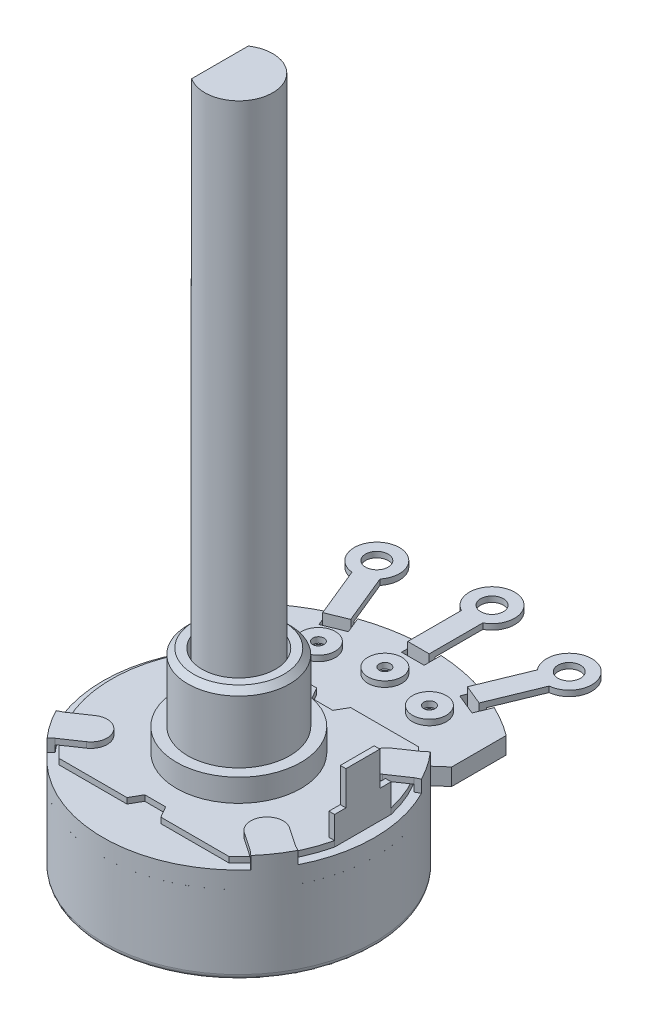
SolidWorks part; units mm, degrees
ref_plane "Front Plane" through (0, 0, 0) normal (0, 0, 1) x (1, 0, 0)
ref_plane "Top Plane" through (0, 0, 0) normal (0, 1, 0) x (1, 0, 0)
ref_plane "Right Plane" through (0, 0, 0) normal (1, 0, 0) x (0, 0, -1)
sketch "Sketch1" plane through (0, 0, 0) normal (0, 1, 0) x (1, 0, 0)
  circle A0 centre (0, 0) radius 12
  dimension "D1" = 24
extrude "Boss-Extrude1" add sketch "Sketch1" along normal blind 7
sketch "Sketch2" plane through (0, 7, 0) normal (0, 1, 0) x (1, 0, 0)
  circle A0 centre (0, 0) radius 11.5
  circle A1 centre (0, 0) radius 12 construction
  dimension "D1" = 0.5
extrude "Cut-Extrude1" cut sketch "Sketch2" against normal blind 6.5
sketch "Sketch3" plane through (0, 7, 0) normal (0, 1, 0) x (1, 0, 0)
  line L0 (0, 0) -> (-13.6067, 12) construction
  line L1 (-13.6067, 12) -> (13.6067, 12) construction
  line L2 (13.6067, 12) -> (0, 0) construction
  line L3 (0, 0) -> (0, 11.5) construction
  line L4 (-9, 7.9373) -> (9, 7.9373) construction
  line L5 (-9, 7.9373) -> (0, 0)
  line L6 (0, 0) -> (9, 7.9373)
  circle A0 centre (0, 0) radius 11.5 construction
  circle A1 centre (0, 0) radius 12 construction
  arc A3 (9, 7.9373) -> (-9, 7.9373) centre (0, 0) ccw
  dimension "D1" = 18
extrude "Cut-Extrude2" cut sketch "Sketch3" against normal blind 2
ref_plane "Plane1" through (0, 7.001, 0) normal (0, 1, 0) x (1, 0, 0)
sketch "Sketch10" plane through (0, 7.001, 0) normal (0, 1, 0) x (1, 0, 0)
  line L0 (-10.2422, 5.2295) -> (-10.6875, 5.4569)
  line L1 (-9, 7.9373) -> (-8.625, 7.6065)
  line L2 (0, 0) -> (-12, 0) construction
  line L3 (-9, 7.9373) -> (-10, 8.8192)
  line L4 (-10, 8.8192) -> (-10, 13.6383)
  line L5 (0, 0) -> (0, 16.9117) construction
  line L6 (9, 7.9373) -> (10, 8.8192)
  line L7 (10, 8.8192) -> (10, 13.6383)
  line L8 (-9, -7.9373) -> (-8.625, -7.6065)
  line L9 (-10.2422, -5.2295) -> (-10.6875, -5.4569)
  line L10 (9, -7.9373) -> (8.625, -7.6065)
  line L11 (10.2422, -5.2295) -> (10.6875, -5.4569)
  line L12 (10.2422, 5.2295) -> (10.6875, 5.4569)
  line L13 (9, 7.9373) -> (8.625, 7.6065)
  line L14 (4.9054, 11.9435) -> (6.4251, 15.6436) construction
  line L15 (0, 0) -> (4.9054, 11.9435) construction
  line L16 (-1, 16.8821) -> (-1, 15.3821)
  line L17 (-1, 15.3821) -> (1, 15.3821)
  line L18 (1, 16.8821) -> (1, 15.3821)
  line L19 (5.4888, 15.9962) -> (4.9189, 14.6086)
  line L20 (4.9189, 14.6086) -> (6.769, 13.8488)
  line L21 (6.769, 13.8488) -> (7.3388, 15.2363)
  line L22 (-6.769, 13.8488) -> (-7.3388, 15.2363)
  line L23 (-4.9189, 14.6086) -> (-6.769, 13.8488)
  line L24 (-5.4888, 15.9962) -> (-4.9189, 14.6086)
  arc A0 (-10.6875, 5.4569) -> (-10.6875, -5.4569) centre (0, 0) ccw
  arc A1 (10, 13.6383) -> (7.3388, 15.2363) centre (0, 0) ccw
  circle A2 centre (0, 0) radius 12.9117 construction
  circle A3 centre (0, 12.9117) radius 0.5
  circle A4 centre (-4.9054, 11.9435) radius 0.5
  circle A5 centre (4.9054, 11.9435) radius 0.5
  arc A6 (-8.625, 7.6065) -> (-10.2422, 5.2295) centre (0, 0) ccw
  arc A7 (-8.625, -7.6065) -> (-10.2422, -5.2295) centre (0, 0) cw
  arc A8 (8.625, -7.6065) -> (10.2422, -5.2295) centre (0, 0) ccw
  arc A9 (8.625, 7.6065) -> (10.2422, 5.2295) centre (0, 0) cw
  arc A10 (10.6875, -5.4569) -> (10.6875, 5.4569) centre (0, 0) ccw
  arc A11 (-9, -7.9373) -> (9, -7.9373) centre (0, 0) ccw
  arc A12 (-1, 16.8821) -> (-5.4888, 15.9962) centre (0, 0) ccw
  arc A13 (5.4888, 15.9962) -> (1, 16.8821) centre (0, 0) ccw
  arc A14 (-7.3388, 15.2363) -> (-10, 13.6383) centre (0, 0) ccw
  dimension "D1" = 4
  dimension "D2" = 1
  dimension "D6" = 3
  dimension "D3" = 20
  dimension "D4" = 4.8192
  dimension "D5" = 4.8192
  dimension "D7" = 5
  dimension "D8" = 5
  dimension "D9" = 1.5
  dimension "D10" = 2
  dimension "D11" = 2
  dimension "D12" = 1.5
  dimension "D13" = 2
  dimension "D14" = 1
extrude "Boss-Extrude2" add sketch "Sketch10" along normal blind 1.5 separate body
sketch "Sketch11" plane through (0, 7, 0) normal (0, 1, 0) x (1, 0, 0)
  line L0 (8.625, 7.6065) -> (9, 7.9373)
  line L1 (10.6895, 5.4529) -> (10.2441, 5.2257)
  line L2 (0, 0) -> (12, 0) construction
  line L3 (8.625, -7.6065) -> (9, -7.9373)
  line L4 (10.6895, -5.4529) -> (10.2441, -5.2257)
  line L5 (0, 0) -> (0, 6) construction
  line L6 (-8.625, -7.6065) -> (-9, -7.9373)
  line L7 (-10.6895, -5.4529) -> (-10.2441, -5.2257)
  line L8 (-10.6895, 5.4529) -> (-10.2441, 5.2257)
  line L9 (-8.625, 7.6065) -> (-9, 7.9373)
  arc A0 (-9, 7.9373) -> (9, 7.9373) centre (0, 0) ccw construction
  arc A1 (-8.625, 7.6065) -> (8.625, 7.6065) centre (0, 0) ccw construction
  arc A2 (10.2441, 5.2257) -> (8.625, 7.6065) centre (0, 0) ccw
  arc A3 (10.6895, 5.4529) -> (9, 7.9373) centre (0, 0) ccw
  arc A4 (10.6895, -5.4529) -> (9, -7.9373) centre (0, 0) cw
  arc A5 (10.2441, -5.2257) -> (8.625, -7.6065) centre (0, 0) cw
  arc A6 (-10.6895, -5.4529) -> (-9, -7.9373) centre (0, 0) ccw
  arc A7 (-10.2441, -5.2257) -> (-8.625, -7.6065) centre (0, 0) ccw
  arc A8 (-10.2441, 5.2257) -> (-8.625, 7.6065) centre (0, 0) cw
  arc A9 (-10.6895, 5.4529) -> (-9, 7.9373) centre (0, 0) cw
  dimension "D1" = 0.5
  dimension "D2" = 6
extrude "Boss-Extrude3" add sketch "Sketch11" along normal blind 2.6
fillet "Fillet1" radius 0.5 1 edges at (0, 0, 12)
ref_plane "Plane2" through (0, 8.511, 0) normal (0, 1, 0) x (1, 0, 0)
sketch "Sketch14" plane through (0, 8.511, 0) normal (0, 1, 0) x (1, 0, 0)
  line L0 (0, 0) -> (-7.5, 0) construction
  line L1 (-7.5, 8.3853) -> (-1.5, 8.3853)
  line L3 (-7.5, -8.3853) -> (-1.5, -8.3853)
  line L5 (0.9226, -7.3853) -> (1.5, -8.3853)
  line L6 (1.5, 8.3853) -> (7.5, 8.3853)
  line L7 (-0.9226, 7.3853) -> (0.9226, 7.3853)
  line L8 (-0.9226, -7.3853) -> (0.9226, -7.3853)
  line L9 (-0.9226, 7.3853) -> (-1.5, 8.3853)
  line L10 (0.9226, 7.3853) -> (1.5, 8.3853)
  line L11 (-0.9226, -7.3853) -> (-1.5, -8.3853)
  line L12 (1.5, -8.3853) -> (7.5, -8.3853)
  arc A0 (-7.5, 8.3853) -> (-7.5, -8.3853) centre (0, 0) ccw
  arc A1 (10.2441, 5.2257) -> (8.625, 7.6065) centre (0, 0) ccw construction
  arc A2 (7.5, -8.3853) -> (7.5, 8.3853) centre (0, 0) ccw
  dimension "D1" = 0.25
  dimension "D2" = 120
  dimension "D3" = 120
  dimension "D4" = 1
  dimension "D5" = 3
  dimension "D6" = 15
  dimension "D7" = 6
extrude "Boss-Extrude4" add sketch "Sketch14" along normal blind 0.5 separate body
sketch "Sketch15" plane through (0, 9.011, 0) normal (0, 1, 0) x (1, 0, 0)
  line L0 (0, 0) -> (11.25, 0) construction
  line L2 (10.9687, 2.5) -> (10.4687, 2.5)
  line L3 (10.9687, 2.5) -> (10.9687, -2.5)
  line L4 (10.9687, -2.5) -> (10.4687, -2.5)
  line L5 (10.4687, 2.5) -> (10.4687, -2.5)
  arc A0 (7.5, -8.3853) -> (7.5, 8.3853) centre (0, 0) ccw construction
  dimension "D1" = 2.5
  dimension "D2" = 0.5
extrude "Boss-Extrude5" add sketch "Sketch15" along normal blind 2
sketch "Sketch17" plane through (0, 9.011, 0) normal (0, 1, 0) x (1, 0, 0)
  line L2 (0, 0) -> (6, 0) construction
  line L5 (10.9687, 2.5) -> (10.9687, -2.5)
  dimension "D1" = 6
extrude "Cut-Extrude7" cut sketch "Sketch17" against normal up to surface (0.51 mm away) up to face at (-4.9054, 8.501, -11.4435)
sketch "Sketch18" plane through (0, 11.011, 0) normal (0, 1, 0) x (1, 0, 0)
  line L0 (10.4687, 0) -> (10.9687, 0) construction
  line L1 (10.4687, 2.5) -> (10.4687, -2.5) construction
  line L2 (10.9687, -2.5) -> (10.9687, 2.5) construction
  line L3 (10.4687, 2.5) -> (10.4687, -2.5) construction
  line L4 (10.4687, 1.5) -> (10.9687, 1.5)
  line L5 (10.4687, 1.5) -> (10.4687, -1.5)
  line L6 (10.4687, -1.5) -> (10.9687, -1.5)
  line L7 (10.9687, 1.5) -> (10.9687, -1.5)
  point P12 (10.4687, 0)
  dimension "D1" = 3
extrude "Boss-Extrude6" add sketch "Sketch18" along normal blind 3
ref_plane "Plane5" through (9.4346, 0, 6.4161) normal (-0.8269, 0, -0.5623) x (-0.5623, 0, 0.8269)
sketch "Sketch19" plane through (9.4346, 0, 6.4161) normal (-0.8269, 0, -0.5623) x (-0.5623, 0, 0.8269)
  line L0 (1.4396, 9.6) -> (1.4396, 8.501) construction
  line L1 (-1.4396, 9.6) -> (1.4396, 9.6)
  line L2 (-1.4396, 9.6) -> (-1.4396, 9.1)
  line L3 (-1.4396, 9.1) -> (1.4396, 9.1)
  line L4 (1.4396, 9.6) -> (1.4396, 9.1)
  dimension "D1" = 0.5
extrude "Boss-Extrude7" add sketch "Sketch19" along normal blind 2 and the other way blind 0.25 separate body
sketch "Sketch21" plane through (0, 9.6, 0) normal (0, 1, 0) x (1, 0, 0)
  line L0 (6.9712, -6.4818) -> (8.5903, -4.101) construction
  line L1 (8.5903, -4.101) -> (6.9712, -6.4818)
  arc A0 (8.5903, -4.101) -> (6.9712, -6.4818) centre (7.7808, -5.2914) ccw
extrude "Boss-Extrude8" add sketch "Sketch21" against normal up to surface (0.5 mm away) up to face at (8.711, 9.1, 5.924)
ref_plane "Plane7" through (-9.4346, 0, -6.4161) normal (0.8269, 0, 0.5623) x (0.5623, 0, -0.8269)
sketch "Sketch34" plane through (-9.4346, 0, -6.4161) normal (0.8269, 0, 0.5623) x (0.5623, 0, -0.8269)
  line L0 (-1.4396, 9.6) -> (-1.4396, 8.501) construction
  line L1 (1.4396, 9.6) -> (-1.4396, 9.6)
  line L2 (1.4396, 9.6) -> (1.4396, 9.1)
  line L3 (1.4396, 9.1) -> (-1.4396, 9.1)
  line L4 (-1.4396, 9.6) -> (-1.4396, 9.1)
  dimension "D1" = 0.5
extrude "Boss-Extrude18" add sketch "Sketch34" along normal blind 2 and the other way blind 0.3 separate body
ref_plane "Plane8" through (9.4346, 0, -6.4161) normal (-0.8269, 0, 0.5623) x (0.5623, 0, 0.8269)
sketch "Sketch35" plane through (9.4346, 0, -6.4161) normal (-0.8269, 0, 0.5623) x (0.5623, 0, 0.8269)
  line L0 (1.4396, 9.6) -> (1.4396, 8.501) construction
  line L1 (-1.4396, 9.6) -> (1.4396, 9.6)
  line L2 (-1.4396, 9.6) -> (-1.4396, 9.1)
  line L3 (-1.4396, 9.1) -> (1.4396, 9.1)
  line L4 (1.4396, 9.6) -> (1.4396, 9.1)
  dimension "D1" = 0.5
extrude "Boss-Extrude19" add sketch "Sketch35" along normal blind 2 and the other way blind 0.25
ref_plane "Plane9" through (-9.4346, 0, 6.4161) normal (-0.8269, 0, 0.5623) x (0.5623, 0, 0.8269)
sketch "Sketch36" plane through (-9.4346, 0, 6.4161) normal (-0.8269, 0, 0.5623) x (0.5623, 0, 0.8269)
  line L0 (-1.4396, 9.6) -> (-1.4396, 8.501) construction
  line L1 (1.4396, 9.6) -> (-1.4396, 9.6)
  line L2 (1.4396, 9.6) -> (1.4396, 9.1)
  line L3 (1.4396, 9.1) -> (-1.4396, 9.1)
  line L4 (-1.4396, 9.6) -> (-1.4396, 9.1)
  dimension "D1" = 0.5
extrude "Boss-Extrude20" add sketch "Sketch36" against normal blind 2 and the other way blind 0.25
sketch "Sketch37" plane through (0, 9.6, 0) normal (0, 1, 0) x (1, 0, 0)
  line L0 (-6.9712, -6.4818) -> (-8.5903, -4.101) construction
  line L1 (-6.9712, 6.4818) -> (-8.5903, 4.101) construction
  line L2 (8.5903, 4.101) -> (6.9712, 6.4818) construction
  line L3 (6.9712, 6.4818) -> (8.5903, 4.101)
  line L5 (-6.9712, 6.4818) -> (-8.5903, 4.101)
  line L7 (-8.5903, -4.101) -> (-6.9712, -6.4818)
  arc A0 (-6.9712, -6.4818) -> (-8.5903, -4.101) centre (-7.7808, -5.2914) ccw
  arc A1 (-8.5903, 4.101) -> (-6.9712, 6.4818) centre (-7.7808, 5.2914) ccw
  arc A2 (6.9712, 6.4818) -> (8.5903, 4.101) centre (7.7808, 5.2914) ccw
extrude "Boss-Extrude21" add sketch "Sketch37" against normal up to surface (0.5 mm away) up to face at (-8.7317, 9.1, -5.9381)
sketch "Sketch22" plane through (0, 9.011, 0) normal (0, 1, 0) x (1, 0, 0)
  circle A0 centre (0, 0) radius 5.5
  dimension "D1" = 11
extrude "Boss-Extrude9" add sketch "Sketch22" along normal blind 2
sketch "Sketch23" plane through (0, 11.011, 0) normal (0, 1, 0) x (1, 0, 0)
  circle A0 centre (0, 0) radius 3.25
  circle A1 centre (0, 0) radius 4.5
  dimension "D1" = 9
  dimension "D2" = 6.5
extrude "Boss-Extrude10" add sketch "Sketch23" along normal blind 6
chamfer "Chamfer1" distance 0.5 angle 45 1 edges at (0, 17.011, 4.5)
sketch "Sketch24" plane through (0, 11.011, 0) normal (0, 1, 0) x (1, 0, 0)
  circle A0 centre (0, 0) radius 3
  dimension "D1" = 6
extrude "Boss-Extrude11" add sketch "Sketch24" along normal blind 50
sketch "Sketch25" plane through (0, 61.011, 0) normal (0, 1, 0) x (1, 0, 0)
  line L4 (-1.6583, 2.5) -> (-1.6583, -2.5)
  arc A0 (-1.6583, 2.5) -> (-1.6583, -2.5) centre (0, 0) ccw
  dimension "D2" = 6
  dimension "D1" = 5
extrude "Cut-Extrude8" cut sketch "Sketch25" against normal blind 16
sketch "Sketch26" plane through (0, 7.001, 0) normal (0, -1, 0) x (1, 0, 0)
  line L1 (-5.7841, -11.5826) -> (-7.1026, -14.7928)
  line L2 (-7.1026, -14.7928) -> (-5.3451, -15.5147)
  line L3 (-5.3451, -15.5147) -> (-4.0266, -12.3045)
  line L4 (-0.95, -12.9117) -> (-0.95, -16.3821)
  line L5 (-0.95, -16.3821) -> (0.95, -16.3821)
  line L6 (0.95, -16.3821) -> (0.95, -12.9117)
  line L7 (4.0266, -12.3045) -> (5.3451, -15.5147)
  line L8 (5.3451, -15.5147) -> (7.1026, -14.7928)
  line L9 (7.1026, -14.7928) -> (5.7841, -11.5826)
  line L10 (-6.769, -13.8488) -> (-7.3388, -15.2363) construction
  line L11 (-5.4888, -15.9962) -> (-4.9189, -14.6086) construction
  line L12 (-1, -15.3821) -> (-1, -16.8821) construction
  line L13 (1, -16.8821) -> (1, -15.3821) construction
  line L14 (4.9189, -14.6086) -> (5.4888, -15.9962) construction
  line L15 (-4.9189, -14.6086) -> (-6.769, -13.8488) construction
  line L16 (1, -15.3821) -> (-1, -15.3821) construction
  line L17 (6.769, -13.8488) -> (4.9189, -14.6086) construction
  arc A0 (-4.0266, -12.3045) -> (-5.7841, -11.5826) centre (-4.9054, -11.9435) ccw
  arc A1 (0.95, -12.9117) -> (-0.95, -12.9117) centre (0, -12.9117) ccw
  arc A2 (5.7841, -11.5826) -> (4.0266, -12.3045) centre (4.9054, -11.9435) ccw
  dimension "D1" = 1.9
  dimension "D2" = 1
  dimension "1.9" = 1.9
  dimension "D3" = 1.9
  dimension "D4" = 1
  dimension "D5" = 1
extrude "Boss-Extrude12" add sketch "Sketch26" along normal blind 0.5
sketch "Sketch27" plane through (0, 7.001, 0) normal (0, 1, 0) x (1, 0, 0)
  line L0 (-0.95, 15.3821) -> (-0.95, 16.3821) construction
  line L1 (0.95, 16.3821) -> (-0.95, 16.3821)
  line L2 (0.95, 16.3821) -> (0.95, 15.8821)
  line L3 (0.95, 15.8821) -> (-0.95, 15.8821)
  line L4 (-0.95, 16.3821) -> (-0.95, 15.8821)
  line L5 (-5.3451, 15.5147) -> (-5.1551, 15.0522)
  line L6 (-5.3451, 15.5147) -> (-4.9652, 14.5896) construction
  line L7 (-5.1551, 15.0522) -> (-6.9127, 14.3303)
  line L8 (-6.7227, 13.8678) -> (-7.1026, 14.7928) construction
  line L9 (-6.9127, 14.3303) -> (-7.1026, 14.7928)
  line L10 (-7.1026, 14.7928) -> (-5.3451, 15.5147)
  line L11 (7.1026, 14.7928) -> (6.9127, 14.3303)
  line L12 (7.1026, 14.7928) -> (6.7227, 13.8678) construction
  line L13 (6.9127, 14.3303) -> (5.1551, 15.0522)
  line L14 (4.9652, 14.5896) -> (5.3451, 15.5147) construction
  line L15 (5.1551, 15.0522) -> (5.3451, 15.5147)
  line L16 (5.3451, 15.5147) -> (7.1026, 14.7928)
  dimension "D1" = 0.5
  dimension "D2" = 0.5
  dimension "D3" = 0.5
extrude "Boss-Extrude13" add sketch "Sketch27" along normal blind 2.1
sketch "Sketch28" plane through (6.2239, 0, -15.1537) normal (0.3799, 0, -0.925) x (-0.925, 0, -0.3799)
  line L0 (0.95, 6.501) -> (0.95, 9.101) construction
  line L1 (-0.95, 9.101) -> (0.95, 9.101)
  line L2 (-0.95, 9.101) -> (-0.95, 8.601)
  line L3 (-0.95, 8.601) -> (0.95, 8.601)
  line L4 (0.95, 9.101) -> (0.95, 8.601)
  dimension "D1" = 0.5
extrude "Boss-Extrude14" add sketch "Sketch28" along normal blind 8
sketch "Sketch29" plane through (0, 0, -16.3821) normal (0, 0, -1) x (-1, 0, 0)
  line L0 (0.95, 6.501) -> (0.95, 9.101) construction
  line L1 (-0.95, 9.101) -> (0.95, 9.101)
  line L2 (-0.95, 9.101) -> (-0.95, 8.601)
  line L3 (-0.95, 8.601) -> (0.95, 8.601)
  line L4 (0.95, 9.101) -> (0.95, 8.601)
  dimension "D1" = 0.5
extrude "Boss-Extrude15" add sketch "Sketch29" along normal blind 8
sketch "Sketch30" plane through (-6.2239, 0, -15.1537) normal (-0.3799, 0, -0.925) x (-0.925, 0, 0.3799)
  line L0 (0.95, 6.501) -> (0.95, 9.101) construction
  line L1 (-0.95, 9.101) -> (0.95, 9.101)
  line L2 (-0.95, 9.101) -> (-0.95, 8.601)
  line L3 (-0.95, 8.601) -> (0.95, 8.601)
  line L4 (0.95, 9.101) -> (0.95, 8.601)
  dimension "D1" = 0.5
extrude "Boss-Extrude16" add sketch "Sketch30" along normal blind 8
sketch "Sketch31" plane through (0, 9.101, 0) normal (0, 1, 0) x (1, 0, 0)
  line L0 (8.3844, 22.9148) -> (10.142, 22.193) construction
  line L1 (-10.142, 22.193) -> (-8.3844, 22.9148) construction
  line L2 (-0.95, 24.3821) -> (0.95, 24.3821) construction
  line L3 (-9.2632, 22.5539) -> (-8.5034, 20.7039) construction
  line L4 (-5.1551, 15.0522) -> (-8.3844, 22.9148) construction
  line L5 (0, 24.3821) -> (0, 22.3821) construction
  line L6 (9.2632, 22.5539) -> (8.5034, 20.7039) construction
  circle A0 centre (8.5034, 20.7039) radius 2
  circle A1 centre (0, 22.3821) radius 2
  circle A2 centre (-8.5034, 20.7039) radius 2
  circle A3 centre (-4.9054, 11.9435) radius 1.5
  circle A4 centre (0, 12.9117) radius 1.5
  circle A5 centre (4.9054, 11.9435) radius 1.5
  circle A6 centre (-4.9054, 11.9435) radius 0.5
  circle A7 centre (0, 12.9117) radius 0.5
  circle A8 centre (4.9054, 11.9435) radius 0.5
  dimension "D1" = 4
  dimension "D2" = 4
  dimension "D3" = 4
  dimension "D4" = 3
  dimension "D5" = 3
  dimension "D6" = 3
  dimension "D7" = 1
  dimension "D8" = 1
  dimension "D9" = 1
extrude "Boss-Extrude17" add sketch "Sketch31" against normal up to surface (0.5 mm away) up to face at (-7.7435, 8.601, -18.8538)
sketch "Sketch33" plane through (0, 9.101, 0) normal (0, 1, 0) x (1, 0, 0)
  line L0 (8.2932, 22.6928) -> (8.3844, 22.9148)
  line L1 (8.3844, 22.9148) -> (10.142, 22.193)
  line L2 (10.142, 22.193) -> (10.0508, 21.971)
  line L3 (-0.95, 24.142) -> (-0.95, 24.3821)
  line L4 (-0.95, 24.3821) -> (0.95, 24.3821)
  line L5 (0.95, 24.3821) -> (0.95, 24.142)
  line L6 (-10.0508, 21.971) -> (-10.142, 22.193)
  line L7 (-10.142, 22.193) -> (-8.3844, 22.9148)
  line L8 (-8.3844, 22.9148) -> (-8.2932, 22.6928)
  circle A0 centre (-8.5034, 20.7039) radius 1
  circle A1 centre (0, 22.3821) radius 1
  circle A2 centre (8.5034, 20.7039) radius 1
  arc A3 (-8.2932, 22.6928) -> (-10.0508, 21.971) centre (-8.5034, 20.7039) ccw
  arc A4 (0.95, 24.142) -> (-0.95, 24.142) centre (0, 22.3821) ccw
  arc A5 (10.0508, 21.971) -> (8.2932, 22.6928) centre (8.5034, 20.7039) ccw
  circle A6 centre (-4.9054, 11.9435) radius 0.5
  circle A7 centre (0, 12.9117) radius 0.5
  circle A8 centre (4.9054, 11.9435) radius 0.5
  line M1 (-8.2932, 22.6928) -> (-8.3844, 22.9148)
  line M2 (-8.3844, 22.9148) -> (-10.142, 22.193)
  line M3 (-10.142, 22.193) -> (-10.0508, 21.971)
  dimension "D1" = 2
  dimension "D2" = 2
  dimension "D3" = 2
  dimension "D4" = 1
  dimension "D5" = 1
  dimension "D6" = 1
extrude "Cut-Extrude9" cut sketch "Sketch33" against normal through all contours A0 | A3 L7 M3 | A3 M1 M2 | A1 | A2 | A5 L1 L0 | A5 L2 L1 | A4 L5 L4 | A4 L4 L3 | A7 | A8 | A6
